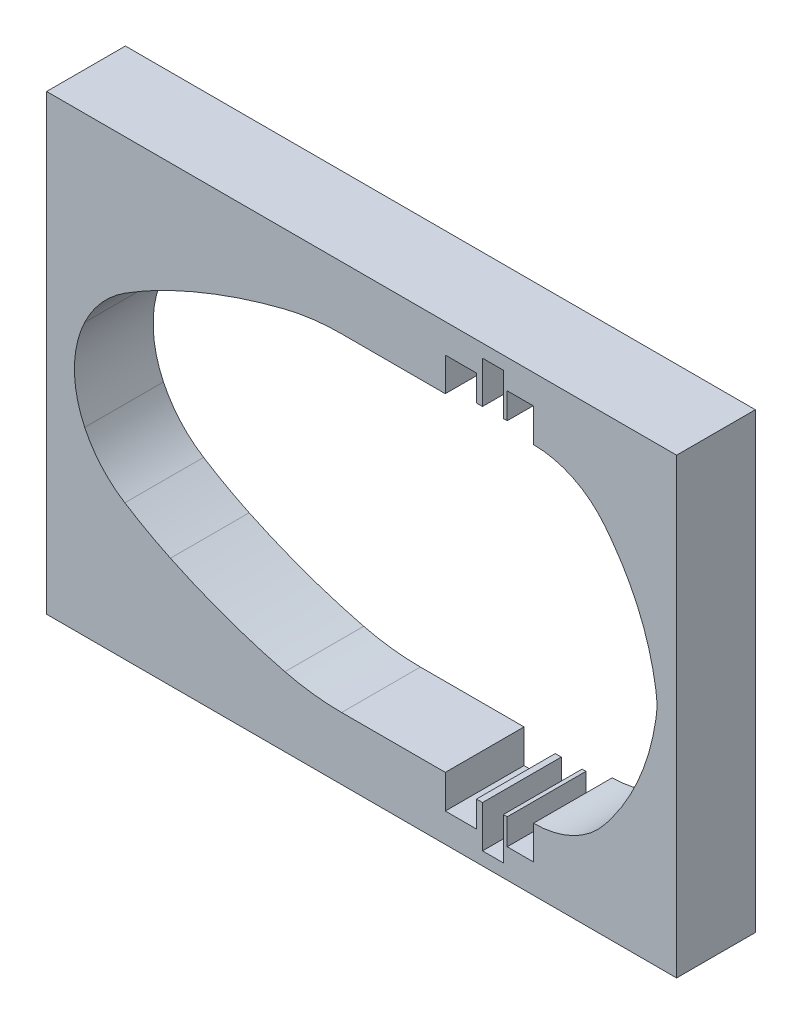
SolidWorks part; units mm, degrees
ref_plane "前基準面" through (0, 0, 0) normal (0, 0, 1) x (1, 0, 0)
ref_plane "上基準面" through (0, 0, 0) normal (0, 1, 0) x (1, 0, 0)
ref_plane "右基準面" through (0, 0, 0) normal (1, 0, 0) x (0, 0, -1)
sketch "草圖2" plane through (0, 0, 0) normal (0, 0, 1) x (1, 0, 0)
  line L0 (-46.4388, 70.8926) -> (220.2278, 70.8926) construction
  line L1 (-105.3201, 72.5991) -> (290.3658, 72.5991) construction
  line L3 (9.5822, 114.2394) -> (32.6396, 114.2394)
  line L4 (32.6396, 114.2394) -> (35.912, 114.2394)
  line L5 (35.912, 114.2394) -> (35.912, 122.7488)
  line L6 (35.912, 122.7488) -> (43.825, 122.7488)
  line L7 (43.825, 122.7488) -> (43.825, 116.1506)
  line L8 (43.825, 116.1506) -> (45.3655, 116.1506)
  line L9 (45.3655, 116.1506) -> (45.3655, 126.7874)
  line L10 (45.3655, 126.7874) -> (50.6502, 126.7874)
  line L11 (50.6502, 126.7874) -> (50.6502, 116.1506)
  line L12 (50.6502, 116.1506) -> (51.6326, 116.1506)
  line L13 (51.6326, 116.1506) -> (51.6326, 122.7488)
  line L14 (51.6326, 122.7488) -> (58.3023, 122.7488)
  line L15 (58.3023, 122.7488) -> (58.3023, 114.2394)
  line L16 (89.3434, 76.1268) -> (89.4509, 75.4079)
  line L17 (89.3434, 69.0713) -> (89.4509, 69.7903)
  line L18 (58.3023, 22.4494) -> (58.3023, 30.9588)
  line L19 (51.6326, 22.4494) -> (58.3023, 22.4494)
  line L20 (51.6326, 29.0476) -> (51.6326, 22.4494)
  line L21 (50.6502, 29.0476) -> (51.6326, 29.0476)
  line L22 (50.6502, 18.4108) -> (50.6502, 29.0476)
  line L23 (45.3655, 18.4108) -> (50.6502, 18.4108)
  line L24 (45.3655, 29.0476) -> (45.3655, 18.4108)
  line L25 (43.825, 29.0476) -> (45.3655, 29.0476)
  line L26 (43.825, 22.4494) -> (43.825, 29.0476)
  line L27 (35.912, 22.4494) -> (43.825, 22.4494)
  line L28 (35.912, 30.9588) -> (35.912, 22.4494)
  line L29 (32.6396, 30.9588) -> (35.912, 30.9588)
  line L30 (9.5822, 30.9588) -> (32.6396, 30.9588)
  arc A1 (-45.4817, 95.653) -> (-33.9004, 102.0463) centre (13.2691, 2.9136) cw
  arc A2 (-33.9004, 102.0463) -> (-4.818, 112.4717) centre (32.6396, -37.7959) cw
  arc A3 (-4.818, 112.4717) -> (9.5822, 114.2394) centre (9.5822, 54.703) cw
  arc A4 (58.3023, 114.2394) -> (76.3982, 105.4778) centre (58.3023, 91.1712) cw
  arc A5 (76.3982, 105.4778) -> (78.3509, 102.9079) centre (10.4589, 53.3467) cw
  arc A6 (78.3509, 102.9079) -> (89.3434, 76.1268) centre (29.3855, 67.1631) cw
  arc A7 (89.4509, 75.4079) -> (89.4509, 69.7903) centre (70.6632, 72.5991) cw
  arc A8 (78.3509, 42.2903) -> (89.3434, 69.0713) centre (29.3855, 78.0351) ccw
  arc A9 (76.3982, 39.7204) -> (78.3509, 42.2903) centre (10.4589, 91.8515) ccw
  arc A10 (58.3023, 30.9588) -> (76.3982, 39.7204) centre (58.3023, 54.0269) ccw
  arc A11 (-4.818, 32.7265) -> (9.5822, 30.9588) centre (9.5822, 90.4952) ccw
  arc A12 (-33.9004, 43.1519) -> (-4.818, 32.7265) centre (32.6396, 182.9941) ccw
  arc A13 (-45.4817, 49.5452) -> (-33.9004, 43.1519) centre (13.2691, 142.2846) ccw
  arc A15 (-45.4817, 95.653) -> (-55.6776, 84.157) centre (-30.6332, 72.2143) ccw
  arc A16 (-55.6776, 84.157) -> (-55.6776, 61.0412) centre (-31.4402, 72.5991) ccw
  arc A17 (-45.4817, 49.5452) -> (-55.6776, 61.0412) centre (-30.6332, 72.9839) cw
  point P62 (-51.3914, 90.6249)
  point P64 (-53.497, 72.5991)
  point P65 (-51.3914, 54.5733)
  dimension "D1" = 83.2806
sketch "草圖4" plane through (0, 0, 0) normal (0, 0, 1) x (1, 0, 0)
  line L0 (-105.3201, 72.5991) -> (290.3658, 72.5991) construction
  line L1 (-65.3403, 130.0991) -> (94.6597, 130.0991)
  line L2 (-65.3403, 130.0991) -> (-65.3403, 15.0991)
  line L3 (-65.3403, 15.0991) -> (94.6597, 15.0991)
  line L4 (94.6597, 130.0991) -> (94.6597, 15.0991)
  arc A0 (89.4509, 69.7903) -> (89.4509, 75.4079) centre (70.6632, 72.5991) ccw construction
  point P9 (89.6597, 72.5991)
  dimension "D1" = 160
  dimension "D2" = 115
  dimension "D3" = 57.5
  dimension "D4" = 5
extrude "填料-伸長1" add sketch "草圖4" along normal blind 20 contours L4 L3 L2 L1
extrude "除料-伸長1" cut sketch "草圖2" along normal blind 20
ref_plane "平面1" through (-66.2, 0, 0) normal (1, 0, 0) x (0, 0, -1)
sketch "草圖6" plane through (-66.2, 0, 0) normal (1, 0, 0) x (0, 0, -1)
  line L0 (-10, 130.0991) -> (-10, 15.0991) construction
  line L1 (-20, 130.0991) -> (0, 130.0991) construction
  line L2 (-20, 15.0991) -> (0, 15.0991) construction
  line L3 (-20, 72.5991) -> (0, 72.5991) construction
  line L4 (-20, 130.0991) -> (-20, 15.0991) construction
  line L5 (0, 130.0991) -> (0, 15.0991) construction
  circle A0 centre (-10, 120.0991) radius 5
  circle A1 centre (-10, 105.0991) radius 5
  circle A2 centre (-10, 40.0991) radius 5
  circle A3 centre (-10, 25.0991) radius 5
  dimension "D1" = 10
  dimension "D2" = 5
  dimension "D5" = 5
sketch "草圖16" plane through (-66.2, 0, 0) normal (1, 0, 0) x (0, 0, -1)
  line L0 (-20, 72.5991) -> (0, 72.5991) construction
  line L1 (-10, 130.0991) -> (-10, 15.0991) construction
  circle A0 centre (-10, 120.0991) radius 5.5
  circle A1 centre (-10, 105.0991) radius 5.5
  circle A2 centre (-10, 40.0991) radius 5.5
  circle A3 centre (-10, 25.0991) radius 5.5
  dimension "D1" = 11
  dimension "D2" = 11
extrude "除料-伸長2" cut sketch "草圖16" along normal blind 15 contours A2 | A1 | A0 | A3
